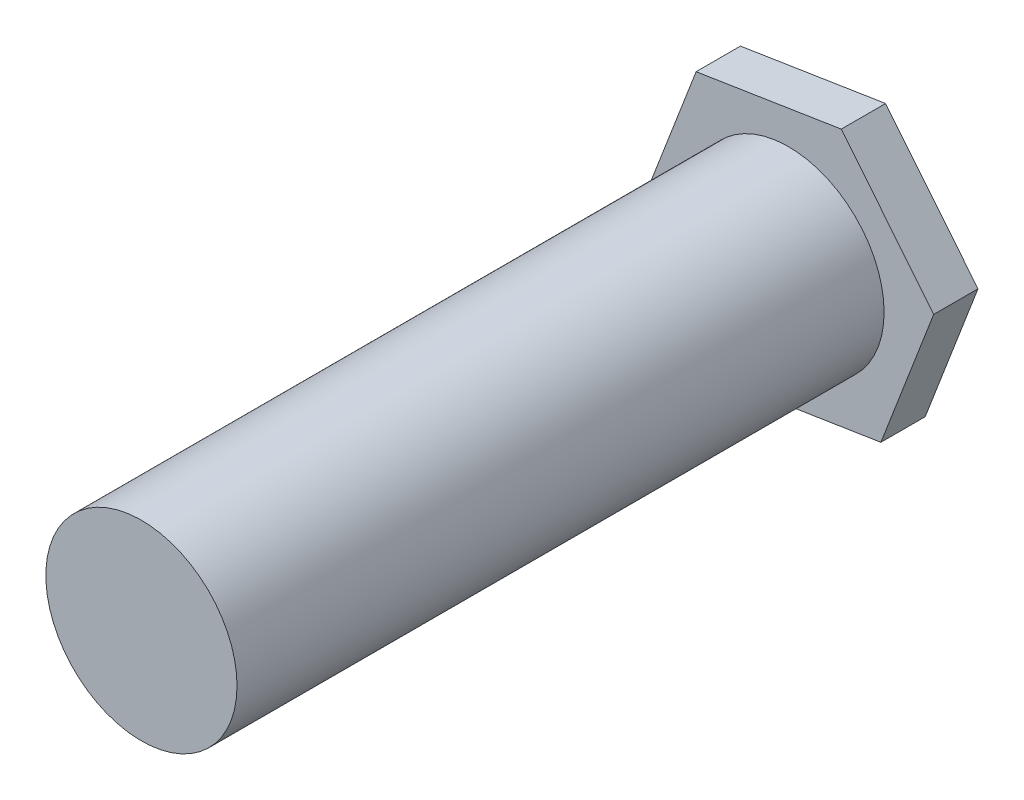
SolidWorks part; units mm, degrees
ref_plane "Front Plane" through (0, 0, 0) normal (0, 0, 1) x (1, 0, 0)
ref_plane "Top Plane" through (0, 0, 0) normal (0, 1, 0) x (1, 0, 0)
ref_plane "Right Plane" through (0, 0, 0) normal (1, 0, 0) x (0, 0, -1)
sketch "Sketch1" plane through (0, 0, 0) normal (0, 0, 1) x (1, 0, 0)
  circle A0 centre (0, 0) radius 2.7392
  circle A1 centre (0, 0) radius 2.7392 construction
  point P4 (0, 0)
extrude "Boss-Extrude1" add sketch "Sketch1" along normal blind 18.034 and the other way blind 0.508
sketch "Sketch2" plane through (0, 0, -0.508) normal (0, 0, -1) x (-1, 0, 0)
  line L1 (2.6475, 3.2753) -> (-1.5127, 3.9305)
  line L2 (-1.5127, 3.9305) -> (-4.1603, 0.6552)
  line L3 (-4.1603, 0.6552) -> (-2.6475, -3.2753)
  line L4 (-2.6475, -3.2753) -> (1.5127, -3.9305)
  line L5 (1.5127, -3.9305) -> (4.1603, -0.6552)
  line L6 (4.1603, -0.6552) -> (2.6475, 3.2753)
  circle A0 centre (0, 0) radius 3.6473 construction
extrude "Boss-Extrude2" add sketch "Sketch2" along normal blind 1.27
